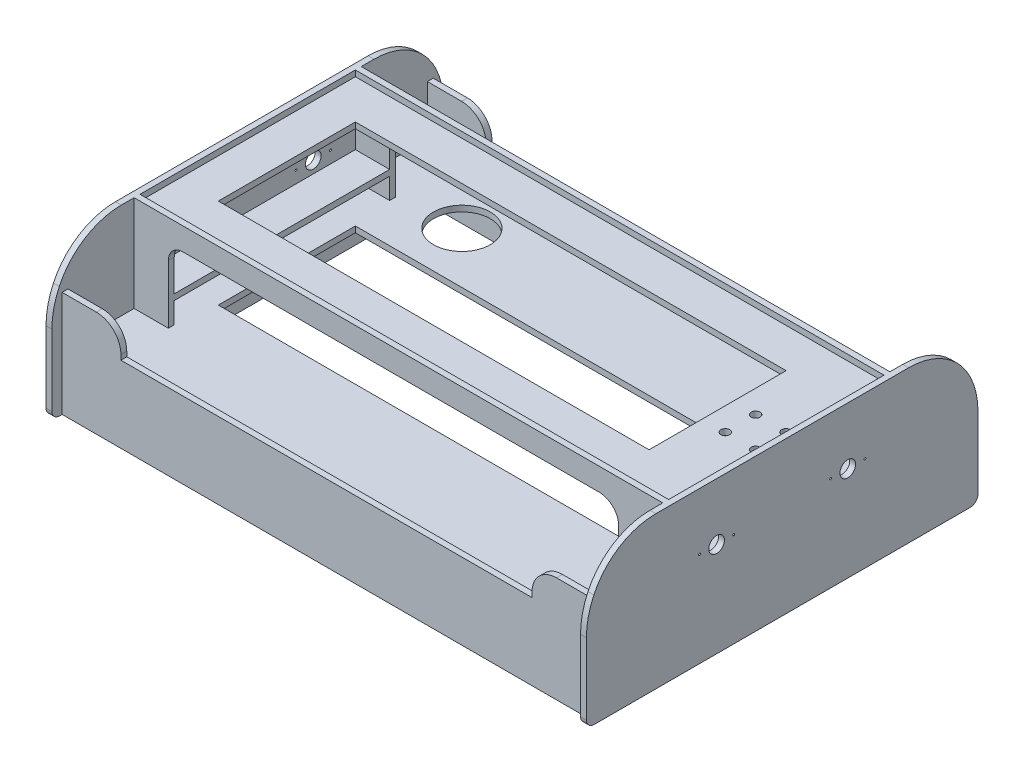
SolidWorks part; units mm, degrees
material "Birch plywood FK"
ref_plane "Спереди" through (0, 0, 0) normal (0, 0, 1) x (1, 0, 0)
ref_plane "Сверху" through (0, 0, 0) normal (0, 1, 0) x (1, 0, 0)
ref_plane "Справа" through (0, 0, 0) normal (1, 0, 0) x (0, 0, -1)
sketch "Эскиз2" plane through (0, 0, 0) normal (0, 1, 0) x (1, 0, 0)
  line L1 (216, -110) -> (-216, -110)
  line L2 (216, -110) -> (216, 110)
  line L3 (216, 110) -> (-216, 110)
  line L4 (-216, -110) -> (-216, 110)
  line L5 (216, -110) -> (-216, 110) construction
  line L6 (216, 110) -> (-216, -110) construction
  point P0 (0, 0)
  dimension "D1" = 220
  dimension "D2" = 432
extrude "Бобышка-Вытянуть2" add sketch "Эскиз2" along normal blind 6
sketch "Эскиз4" plane through (216, 0, 0) normal (1, 0, 0) x (0, 0, -1)
  line L0 (-110, 3) -> (110, 3) construction
  line L1 (-110, 6) -> (-110, 0) construction
  line L2 (110, 6) -> (110, 0) construction
  line L3 (-158, -13) -> (158, -13) construction
  line L4 (-110, -11) -> (-116, -11)
  line L5 (-110, -11) -> (-110, 17)
  line L6 (-110, 17) -> (-116, 17)
  line L7 (-116, -11) -> (-116, 17)
  line L8 (-110, -11) -> (-116, 17) construction
  line L9 (-110, 17) -> (-116, -11) construction
  line L10 (116, -11) -> (110, -11)
  line L11 (116, -11) -> (116, 17)
  line L12 (116, 17) -> (110, 17)
  line L13 (110, -11) -> (110, 17)
  line L14 (116, -11) -> (110, 17) construction
  line L15 (116, 17) -> (110, -11) construction
  point P6 (-113, 3)
  point P11 (113, 3)
  dimension "D1" = 2
extrude "Бобышка-Вытянуть3" add sketch "Эскиз4" against normal up to surface (432 mm away) up to face at (-216, 3, 0)
sketch "Эскиз5" plane through (-216, 0, 0) normal (-1, 0, 0) x (0, 0, 1)
  line L0 (-116, 17) -> (-110, 17)
  line L1 (-110, 17) -> (-110, 6)
  line L2 (-110, 6) -> (110, 6)
  line L3 (110, 6) -> (110, 17)
  line L4 (110, 17) -> (116, 17)
  line L5 (116, 17) -> (116, -11)
  line L6 (116, -11) -> (110, -11)
  line L7 (110, -11) -> (110, 0)
  line L8 (-110, 0) -> (110, 0) construction
  line L9 (110, 0) -> (110, -11) construction
  line L10 (110, 0) -> (-110, 0)
  line L11 (-110, 0) -> (-110, -11)
  line L12 (-110, -11) -> (-116, -11)
  line L13 (-116, -11) -> (-116, 17)
extrude "Бобышка-Вытянуть4" add sketch "Эскиз5" along normal blind 108
sketch "Эскиз6" plane through (0, 17, 0) normal (0, 1, 0) x (1, 0, 0)
  line L1 (216, -116) -> (-324, -116)
  line L2 (216, -116) -> (216, -110)
  line L3 (216, -110) -> (-324, -110)
  line L4 (-324, -116) -> (-324, -110)
  line L5 (216, 116) -> (-324, 116)
  line L6 (216, 116) -> (216, 110)
  line L7 (216, 110) -> (-324, 110)
  line L8 (-324, 116) -> (-324, 110)
extrude "Бобышка-Вытянуть5" add sketch "Эскиз6" along normal blind 25
sketch "Эскиз7" plane through (216, 0, 0) normal (1, 0, 0) x (0, 0, -1)
  line L0 (0, 0) -> (0, 6) construction
  line L1 (-110, 6) -> (110, 6) construction
  line L2 (-200, -143) -> (-200, -23)
  line L3 (-200, -23) -> (-116, 42)
  line L4 (-116, 42) -> (-110, 42) construction
  line L5 (-116, 42) -> (116, 42)
  line L6 (-200, -143) -> (200, -143)
  line L7 (200, -143) -> (200, -23)
  line L8 (200, -23) -> (116, 42)
  point P14 (0, -143)
  point P16 (0, 42)
  dimension "D1" = 120
  dimension "D2" = 200
  dimension "D3" = 185
extrude "Бобышка-Вытянуть6" add sketch "Эскиз7" along normal blind 6
sketch "Эскиз8" plane through (-324, 0, 0) normal (-1, 0, 0) x (0, 0, 1)
  line L0 (-116, 42) -> (-200, -23)
  line L1 (-200, -23) -> (-200, -143)
  line L2 (-200, -143) -> (200, -143)
  line L3 (200, -143) -> (200, -23)
  line L4 (200, -23) -> (116, 42)
  line L5 (116, 42) -> (-116, 42)
extrude "Бобышка-Вытянуть7" add sketch "Эскиз8" along normal blind 6
sketch "Эскиз9" plane through (-324, 0, 0) normal (1, 0, 0) x (0, 0, -1)
  line L0 (0, -83) -> (0, -143) construction
  line L1 (158, -83) -> (-158, -83) construction
  line L2 (-200, -143) -> (200, -143) construction
  line L4 (183.5, -92) -> (-183.5, -92)
  line L5 (183.5, -92) -> (183.5, -86)
  line L6 (183.5, -86) -> (-183.5, -86)
  line L7 (-183.5, -92) -> (-183.5, -86)
  line L8 (183.5, -92) -> (-183.5, -86) construction
  line L9 (183.5, -86) -> (-183.5, -92) construction
  point P6 (0, -89)
  dimension "D1" = 6
  dimension "D2" = 3
  dimension "D3" = 367
extrude "Бобышка-Вытянуть8" add sketch "Эскиз9" along normal up to surface (540 mm away) up to face at (216, -24.3333, 9.1667)
sketch "Эскиз10" plane through (-330, 0, 0) normal (-1, 0, 0) x (0, 0, 1)
  circle A0 centre (67, -46.2762) radius 8
  circle A1 centre (-67, -46.2762) radius 8
  dimension "D1" = 16
extrude "Вырез-Вытянуть1" cut sketch "Эскиз10" against normal through all
sketch "Эскиз11" plane through (222, 0, 0) normal (1, 0, 0) x (0, 0, -1)
  line L0 (-183.5, -89) -> (183.5, -89) construction
  line L1 (-183.5, -86) -> (-183.5, -92) construction
  line L2 (183.5, -92) -> (183.5, -86) construction
  line L3 (-200, -143) -> (200, -143) construction
  line L4 (189.5, -143) -> (183.5, -143)
  line L5 (189.5, -143) -> (189.5, -35)
  line L6 (189.5, -35) -> (183.5, -35)
  line L7 (183.5, -143) -> (183.5, -35)
  line L8 (189.5, -143) -> (183.5, -35) construction
  line L9 (189.5, -35) -> (183.5, -143) construction
  line L10 (-189.5, -143) -> (-183.5, -143)
  line L11 (-189.5, -143) -> (-189.5, -35)
  line L12 (-189.5, -35) -> (-183.5, -35)
  line L13 (-183.5, -143) -> (-183.5, -35)
  line L14 (-189.5, -143) -> (-183.5, -35) construction
  line L15 (-189.5, -35) -> (-183.5, -143) construction
  point P6 (186.5, -89)
  point P11 (-186.5, -89)
extrude "Бобышка-Вытянуть9" add sketch "Эскиз11" against normal up to surface (546 mm away) up to face at (-324, -46.2762, -59)
sketch "Эскиз12" plane through (0, -92, 0) normal (0, -1, 0) x (-1, 0, 0)
  line L0 (324, 0) -> (-216, 0) construction
  line L1 (324, 183.5) -> (324, -183.5) construction
  line L2 (-216, -183.5) -> (-216, 183.5) construction
  line L3 (324, -183.5) -> (-216, -183.5) construction
  line L4 (199, 63.5) -> (269, 63.5)
  line L5 (199, 63.5) -> (199, -63.5)
  line L6 (199, -63.5) -> (269, -63.5)
  line L7 (269, 63.5) -> (269, -63.5)
  line L8 (199, 63.5) -> (269, -63.5) construction
  line L9 (199, -63.5) -> (269, 63.5) construction
  line L10 (-46, 63.5) -> (149, 63.5)
  line L11 (-46, 63.5) -> (-46, -63.5)
  line L12 (-46, -63.5) -> (149, -63.5)
  line L13 (149, 63.5) -> (149, -63.5)
  line L14 (-46, 63.5) -> (149, -63.5) construction
  line L15 (-46, -63.5) -> (149, 63.5) construction
  line L16 (-166, 63.5) -> (-96, 63.5)
  line L17 (-166, 63.5) -> (-166, -63.5)
  line L18 (-166, -63.5) -> (-96, -63.5)
  line L19 (-96, 63.5) -> (-96, -63.5)
  line L20 (-166, 63.5) -> (-96, -63.5) construction
  line L21 (-166, -63.5) -> (-96, 63.5) construction
  point P6 (234, 0)
  point P11 (51.5, 0)
  point P16 (-131, 0)
  dimension "D1" = 55
  dimension "D2" = 50
  dimension "D3" = 50
  dimension "D4" = 50
  dimension "D5" = 120
  dimension "D6" = 195
extrude "Вырез-Вытянуть2" cut sketch "Эскиз12" against normal blind 6
sketch "Эскиз13" plane through (0, -86, 0) normal (0, 1, 0) x (1, 0, 0)
  line L0 (-227.5, 130) -> (-227.5, 114.6) construction
  line L1 (216, 110) -> (216, -110) construction
  line L2 (216, -21.15) -> (173.7, -21.15)
  line L3 (216, -21.15) -> (216, 21.15)
  line L4 (216, 21.15) -> (173.7, 21.15)
  line L5 (173.7, -21.15) -> (173.7, 21.15)
  line L6 (216, -21.15) -> (173.7, 21.15) construction
  line L7 (216, 21.15) -> (173.7, -21.15) construction
  line L8 (211.7574, 21.15) -> (177.9426, 21.15) construction
  circle A0 centre (-227.5, 122.3) radius 29
  point P7 (194.85, 0)
extrude "Вырез-Вытянуть3" cut sketch "Эскиз13" against normal blind 10
sketch "Эскиз14" plane through (216, 0, 0) normal (-1, 0, 0) x (0, 0, 1)
  line L0 (0, 42) -> (0, -143) construction
  line L1 (-116, 42) -> (116, 42) construction
  line L2 (200, -143) -> (-200, -143) construction
  line L4 (-110, -58.5) -> (110, -58.5)
  line L5 (-110, -58.5) -> (-110, -64.5)
  line L6 (-110, -64.5) -> (110, -64.5)
  line L7 (110, -58.5) -> (110, -64.5)
  line L8 (-110, -58.5) -> (110, -64.5) construction
  line L9 (-110, -64.5) -> (110, -58.5) construction
  line L10 (16.9074, -64.5) -> (-16.9074, -64.5) construction
  line L12 (110, 0) -> (110, -11) construction
  point P6 (0, -61.5)
  dimension "D1" = 6
extrude "Бобышка-Вытянуть10" add sketch "Эскиз14" along normal blind 45
sketch "Эскиз15" plane through (0, -58.5, 0) normal (0, 1, 0) x (1, 0, 0)
  circle A0 centre (194.85, 0) radius 16.4
  circle A1 centre (179.35, 15.5) radius 1.5
  circle A2 centre (210.35, 15.5) radius 1.5
  circle A3 centre (210.35, -15.5) radius 1.5
  circle A4 centre (179.35, -15.5) radius 1.5
  circle A5 centre (194.85, 0) radius 16.4 construction
  dimension "D1" = 3
extrude "Вырез-Вытянуть4" cut sketch "Эскиз15" against normal blind 6
sketch "Эскиз16" plane through (0, 6, 0) normal (0, 1, 0) x (1, 0, 0)
  circle A0 centre (179.35, 15.5) radius 4.5
  circle A1 centre (210.35, 15.5) radius 4.5
  circle A2 centre (179.35, -15.5) radius 4.5
  circle A3 centre (210.35, -15.5) radius 4.5
  dimension "D1" = 9
extrude "Вырез-Вытянуть5" cut sketch "Эскиз16" against normal blind 6
fillet "Скругление1" radius 80 4 edges at (-327, -23, -200) (219, -23, -200) (-327, -23, 200) (219, -23, 200)
fillet "Скругление2" radius 8 4 edges at (-327, -143, 200) (219, -143, 200) (-327, -143, -200) (219, -143, -200)
sketch "Эскиз18" plane through (216, 0, 0) normal (-1, 0, 0) x (0, 0, 1)
  line L1 (116, -11) -> (110, -11)
  line L2 (116, -11) -> (116, -86)
  line L3 (116, -86) -> (110, -86)
  line L4 (110, -11) -> (110, -86)
  line L5 (-183.5, -86) -> (183.5, -86) construction
  line L6 (-116, -11) -> (-110, -11)
  line L7 (-116, -11) -> (-116, -86)
  line L8 (-116, -86) -> (-110, -86)
  line L9 (-110, -11) -> (-110, -86)
extrude "Бобышка-Вытянуть11" add sketch "Эскиз18" along normal up to surface (45 mm away) up to face at (171, -61.5, 0)
sketch "Эскиз19" plane through (0, 0, 189.5) normal (0, 0, 1) x (1, 0, 0)
  line L0 (-264, -35) -> (-264, -65)
  line L1 (-324, -35) -> (216, -35) construction
  line L2 (-264, -65) -> (156, -65)
  line L3 (156, -65) -> (156, -35)
  line L4 (216, 1.0201) -> (216, -62.2496) construction
  line L5 (-324, -62.2496) -> (-324, 1.0201) construction
  line L6 (-324, 42) -> (216, 42) construction
  line L7 (-324, 42) -> (216, 42)
  line L8 (-324, 42) -> (-324, 12)
  line L9 (-324, 12) -> (216, 12)
  line L10 (216, 42) -> (216, 12)
  line L13 (-264, -35) -> (156, -35)
  line L14 (-324, 6) -> (216, 6) construction
  line L15 (216, 42) -> (216, 1.0201) construction
  line L16 (-324, 1.0201) -> (-324, 42) construction
  dimension "D1" = 60
  dimension "D2" = 60
  dimension "D3" = 30
  dimension "D6" = 6
extrude "Вырез-Вытянуть8" cut sketch "Эскиз19" against normal through all
fillet "Скругление4" radius 25 4 edges at (-264, -35, -186.5) (156, -35, -186.5) (156, -35, 186.5) (-264, -35, 186.5)
fillet "Скругление6" radius 20 2 edges at (171, -11, 113) (171, -11, -113)
sketch "Эскиз20" plane through (-324, 0, 0) normal (1, 0, 0) x (0, 0, -1)
  line L1 (-116, -11) -> (-110, -11)
  line L2 (-116, -11) -> (-116, -86)
  line L3 (-116, -86) -> (-110, -86)
  line L4 (-110, -11) -> (-110, -86)
  line L5 (116, -11) -> (110, -11)
  line L6 (116, -11) -> (116, -86)
  line L7 (116, -86) -> (110, -86)
  line L8 (110, -11) -> (110, -86)
extrude "Бобышка-Вытянуть12" add sketch "Эскиз20" along normal blind 35
fillet "Скругление7" radius 15 2 edges at (-289, -11, -113) (-289, -11, 113)
sketch "Эскиз21" plane through (-324, 0, 0) normal (1, 0, 0) x (0, 0, -1)
  line L1 (110, -58.5) -> (-110, -58.5)
  line L2 (110, -58.5) -> (110, -64.5)
  line L3 (110, -64.5) -> (-110, -64.5)
  line L4 (-110, -58.5) -> (-110, -64.5)
extrude "Бобышка-Вытянуть13" add sketch "Эскиз21" along normal up to surface (35 mm away) up to face at (-289, -56, 113)
sketch "Эскиз22" plane through (222, 0, 0) normal (1, 0, 0) x (0, 0, -1)
  line L0 (-67, -46.2762) -> (-84.5, -46.2762) construction
  line L3 (-49.5, -46.2762) -> (-67, -46.2762) construction
  line L5 (49.5, -46.2762) -> (67, -46.2762) construction
  line L6 (67, -46.2762) -> (84.5, -46.2762) construction
  circle A0 centre (84.5, -46.2762) radius 1
  circle A1 centre (49.5, -46.2762) radius 1
  circle A2 centre (-49.5, -46.2762) radius 1
  circle A3 centre (-84.5, -46.2762) radius 1
  dimension "D1" = 2
  dimension "D2" = 17.5
extrude "Вырез-Вытянуть9" cut sketch "Эскиз22" against normal through all
sketch "Эскиз23" plane through (0, -86, 0) normal (0, 1, 0) x (1, 0, 0)
  line L0 (174.5142, -138.9) -> (164.5142, -138.9) construction
  line L1 (174.5142, -139.4) -> (164.5142, -139.4)
  line L2 (174.5142, -138.4) -> (164.5142, -138.4)
  line L3 (174.5142, -148.4) -> (164.5142, -148.4) construction
  line L4 (174.5142, -148.9) -> (164.5142, -148.9)
  line L5 (174.5142, -147.9) -> (164.5142, -147.9)
  arc A0 (174.5142, -139.4) -> (174.5142, -138.4) centre (174.5142, -138.9) ccw
  arc A1 (164.5142, -138.4) -> (164.5142, -139.4) centre (164.5142, -138.9) ccw
  arc A2 (174.5142, -148.9) -> (174.5142, -147.9) centre (174.5142, -148.4) ccw
  arc A3 (164.5142, -147.9) -> (164.5142, -148.9) centre (164.5142, -148.4) ccw
  point P2 (169.5142, -138.9)
  point P7 (169.5142, -148.4)
  dimension "D1" = 1
  dimension "D2" = 10
extrude "Вырез-Вытянуть10" cut sketch "Эскиз23" against normal through all
sketch "Эскиз24" plane through (0, 6, 0) normal (0, 1, 0) x (1, 0, 0)
  line L0 (-324, 0) -> (216, 0) construction
  line L1 (-324, -116) -> (-324, 116) construction
  line L2 (216, 116) -> (216, -116) construction
  line L3 (-324, 110) -> (216, 110) construction
  line L4 (156, -70) -> (-284, -70)
  line L5 (156, -70) -> (156, 70)
  line L6 (156, 70) -> (-284, 70)
  line L7 (-284, -70) -> (-284, 70)
  line L8 (156, -70) -> (-284, 70) construction
  line L9 (156, 70) -> (-284, -70) construction
  line L10 (216, -110) -> (216, 110) construction
  point P6 (-64, 0)
  dimension "D1" = 40
  dimension "D2" = 40
  dimension "D3" = 60
extrude "Вырез-Вытянуть11" cut sketch "Эскиз24" against normal through all
sketch "Эскиз25" plane through (-330, 0, 0) normal (-1, 0, 0) x (0, 0, 1)
  line L0 (-116, 42) -> (-168.9587, 1.0201) construction
  line L1 (-154.7692, 12) -> (154.7692, 12)
  line L2 (-154.7692, 12) -> (-154.7692, 42)
  line L3 (-154.7692, 42) -> (154.7692, 42)
  line L4 (154.7692, 12) -> (154.7692, 42)
  line L5 (168.9587, 1.0201) -> (116, 42) construction
  line L7 (-110, 12) -> (110, 12) construction
  line L8 (-116, 42) -> (116, 42) construction
extrude "Вырез-Вытянуть12" cut sketch "Эскиз25" against normal through all
fillet "Скругление8" radius 70 4 edges at (-327, 12, 154.7692) (-327, 12, -154.7692) (219, 12, -154.7692) (219, 12, 154.7692)
